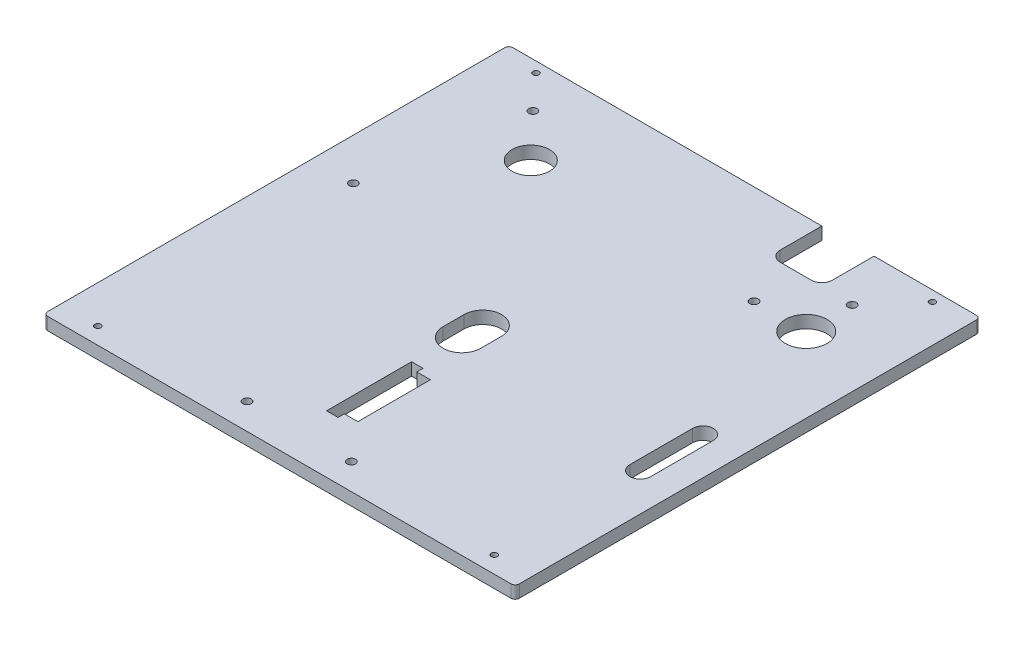
SolidWorks part; units mm, degrees
ref_plane "Front Plane" through (0, 0, 0) normal (0, 0, 1) x (1, 0, 0)
ref_plane "Top Plane" through (0, 0, 0) normal (0, 1, 0) x (1, 0, 0)
ref_plane "Right Plane" through (0, 0, 0) normal (1, 0, 0) x (0, 0, -1)
sketch "Sketch1" plane through (0, 0, 0) normal (0, 1, 0) x (1, 0, 0)
  line L1 (-113, -113) -> (113, -113)
  line L2 (-113, -113) -> (-113, 110)
  line L3 (-113, 110) -> (113, 110)
  line L4 (113, -113) -> (113, 110)
  line L5 (-5, -65) -> (32.7692, -65) construction
  line L6 (-5, -85.375) -> (0.5, -85.375)
  line L7 (-5, -85.375) -> (-5, -44.625)
  line L8 (-5, -44.625) -> (0.5, -44.625)
  line L9 (7, -82.375) -> (7, -47.625)
  line L10 (-3, -85.375) -> (-3, -44.625) construction
  line L11 (0.5, -44.625) -> (0.5, -47.625)
  line L12 (0.5, -47.625) -> (7, -47.625)
  line L13 (-3, -12.5) -> (-3, -22.5) construction
  line L14 (6, -12.5) -> (6, -22.5)
  line L15 (-12, -12.5) -> (-12, -22.5)
  line L16 (7, -82.375) -> (0.5, -82.375)
  line L17 (0.5, -85.375) -> (0.5, -82.375)
  arc A0 (6, -12.5) -> (-12, -12.5) centre (-3, -12.5) ccw
  arc A1 (-12, -22.5) -> (6, -22.5) centre (-3, -22.5) ccw
  circle A2 centre (-95, -105) radius 1.45
  circle A3 centre (-95, 105) radius 1.45
  circle A4 centre (95, 105) radius 1.45
  circle A5 centre (95, -105) radius 1.45
  point P19 (-3, -17.5)
  dimension "D10" = 10
  dimension "D19" = 2.9
  dimension "D2" = 3
  dimension "D3" = 65
  dimension "D4" = 2
  dimension "D5" = 40.75
  dimension "D6" = 10
  dimension "D7" = 3.5
  dimension "D8" = 3
  dimension "D9" = 18
  dimension "D11" = 52.5
  dimension "D12" = 110
  dimension "D13" = 113
  dimension "D14" = 113
  dimension "D15" = 113
  dimension "D16" = 95
  dimension "D17" = 105
  dimension "D18" = 105
  dimension "D20" = 95
extrude "Boss-Extrude1" add sketch "Sketch1" along normal blind 6
sketch "Sketch2" plane through (0, 6, 0) normal (0, 1, 0) x (1, 0, 0)
  line L0 (-28, -100.5) -> (22, -100.5) construction
  line L1 (-3, -100.5) -> (-3, -12.5) construction
  line L2 (95, -35) -> (95, -5) construction
  line L3 (90, -35) -> (90, -5)
  line L4 (100, -35) -> (100, -5)
  line L5 (113, 110) -> (-113, 110) construction
  line L6 (62, 110) -> (37, 110)
  line L7 (62, 110) -> (62, 85)
  line L8 (62, 85) -> (37, 85)
  line L9 (37, 110) -> (37, 85)
  circle A0 centre (-28, -100.5) radius 2
  circle A1 centre (22, -100.5) radius 2
  circle A2 centre (-80, 88.5) radius 2
  circle A3 centre (77, 84.5) radius 2
  circle A4 centre (-93, 15.5) radius 2
  circle A5 centre (52, 62.5) radius 2
  circle A6 centre (-60, 67.5) radius 9
  circle A7 centre (77, 62.5) radius 10
  arc A8 (90, -35) -> (100, -35) centre (95, -35) ccw
  arc A9 (100, -5) -> (90, -5) centre (95, -5) ccw
  point P22 (95, -20)
  dimension "D1" = 4
  dimension "D14" = 18
  dimension "D15" = 20
  dimension "D2" = 50
  dimension "D3" = 88
  dimension "D4" = 101
  dimension "D5" = 77
  dimension "D6" = 97
  dimension "D7" = 80
  dimension "D8" = 55
  dimension "D9" = 75
  dimension "D10" = 28
  dimension "D11" = 90
  dimension "D12" = 57
  dimension "D13" = 80
  dimension "D16" = 10
  dimension "D17" = 30
  dimension "D18" = 95
  dimension "D19" = 20
  dimension "D20" = 85
  dimension "D21" = 65
  dimension "D22" = 40
extrude "Cut-Extrude1" cut sketch "Sketch2" against normal through all
fillet "Fillet1" radius 5 2 edges at (62, 3, -85) (37, 3, -85)
fillet "Fillet2" radius 2 4 edges at (113, 3, -110) (-113, 3, -110) (-113, 3, 113) (113, 3, 113)
